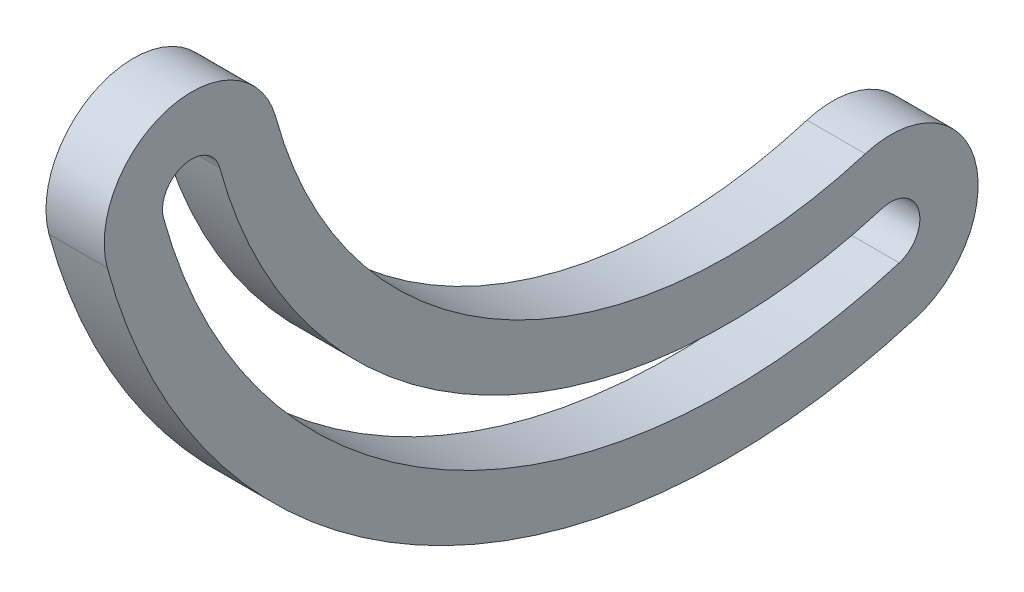
SolidWorks part; units mm, degrees
ref_plane "Front Plane" through (0, 0, 0) normal (0, 0, 1) x (1, 0, 0)
ref_plane "Top Plane" through (0, 0, 0) normal (0, 1, 0) x (1, 0, 0)
ref_plane "Right Plane" through (0, 0, 0) normal (1, 0, 0) x (0, 0, -1)
sketch "Sketch2" plane through (0, 0, 0) normal (1, 0, 0) x (0, 0, -1)
  arc A0 (0, 0) -> (76.2, -42.1422) centre (58.5323, 15.8739) ccw construction
  arc A1 (-9.1929, -2.4931) -> (78.9748, -51.254) centre (58.5323, 15.8739) ccw
  arc A2 (9.1929, 2.4931) -> (73.4252, -33.0303) centre (58.5323, 15.8739) ccw
  arc A3 (9.1929, 2.4931) -> (-9.1929, -2.4931) centre (0, 0) ccw
  arc A4 (78.9748, -51.254) -> (73.4252, -33.0303) centre (76.2, -42.1422) ccw
  arc A5 (0, 0) -> (76.2, -42.1422) centre (58.5323, 15.8739) ccw construction
  arc A6 (-3.0643, -0.831) -> (77.1249, -45.1794) centre (58.5323, 15.8739) ccw
  arc A7 (3.0643, 0.831) -> (75.2751, -39.1049) centre (58.5323, 15.8739) ccw
  arc A8 (3.0643, 0.831) -> (-3.0643, -0.831) centre (0, 0) ccw
  arc A9 (77.1249, -45.1794) -> (75.2751, -39.1049) centre (76.2, -42.1422) ccw
  point P3 (29.1815, -37.1972)
  point P9 (29.1815, -37.1972)
  dimension "D1" = 19.05
  dimension "D3" = 6.35
  dimension "D2" = 76.2
extrude "Boss-Extrude1" add sketch "Sketch2" along normal blind 6.35
